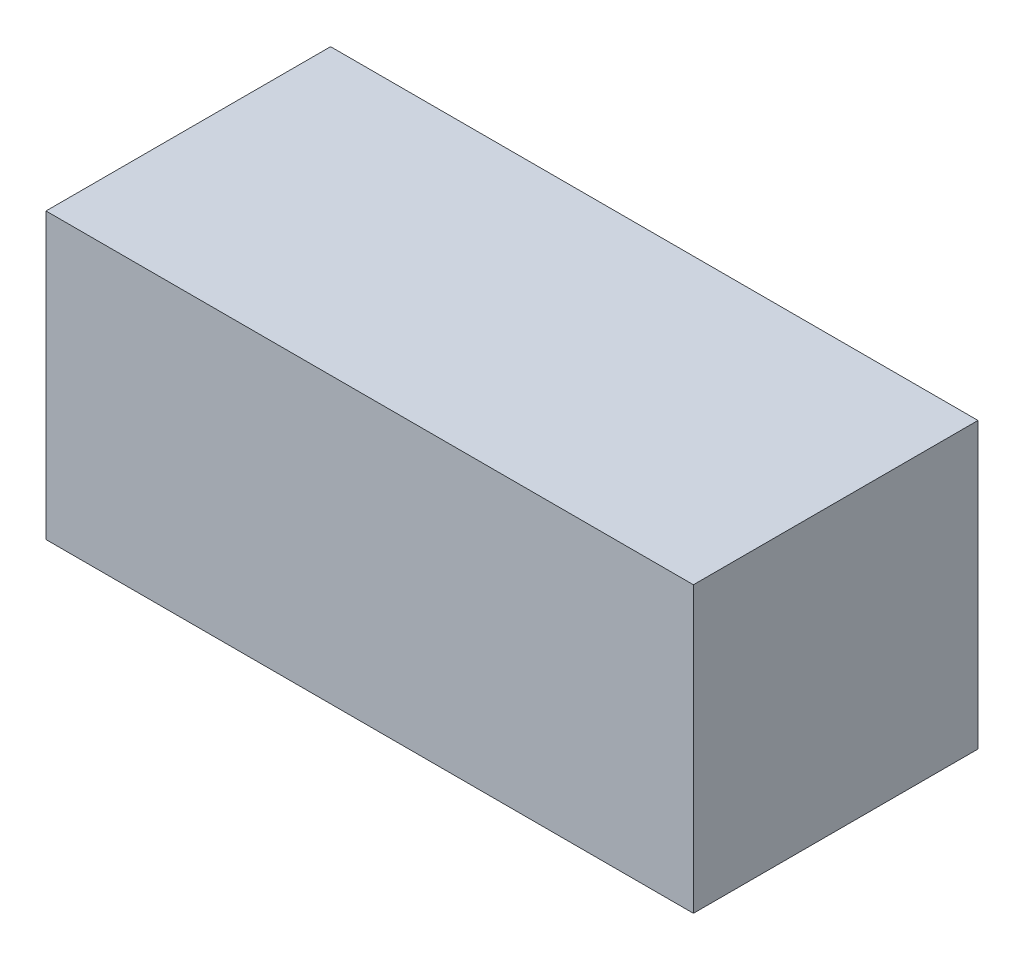
SolidWorks part; units mm, degrees
ref_plane "Front Plane" through (0, 0, 0) normal (0, 0, 1) x (1, 0, 0)
ref_plane "Top Plane" through (0, 0, 0) normal (0, 1, 0) x (1, 0, 0)
ref_plane "Right Plane" through (0, 0, 0) normal (1, 0, 0) x (0, 0, -1)
sketch "Sketch1" plane through (0, 0, 0) normal (0, 1, 0) x (1, 0, 0)
  line L1 (-568.75, 250) -> (568.75, 250)
  line L2 (-568.75, 250) -> (-568.75, -250)
  line L3 (-568.75, -250) -> (568.75, -250)
  line L4 (568.75, 250) -> (568.75, -250)
  line L5 (-568.75, 250) -> (568.75, -250) construction
  line L6 (-568.75, -250) -> (568.75, 250) construction
  point P0 (0, 0)
  dimension "D1" = 1137.5
  dimension "D2" = 500
extrude "Boss-Extrude1" add sketch "Sketch1" along normal blind 500
